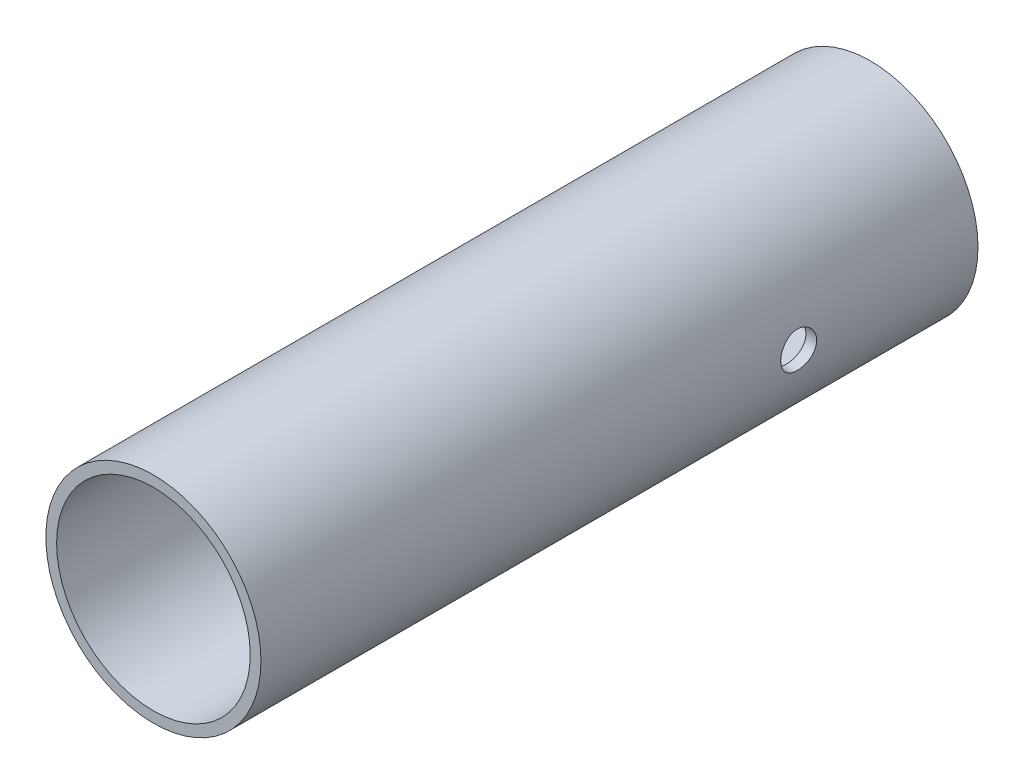
SolidWorks part; units mm, degrees
ref_plane "Płaszczyzna przednia" through (0, 0, 0) normal (0, 0, 1) x (1, 0, 0)
ref_plane "Płaszczyzna górna" through (0, 0, 0) normal (0, 1, 0) x (1, 0, 0)
ref_plane "Płaszczyzna prawa" through (0, 0, 0) normal (1, 0, 0) x (0, 0, -1)
sketch "Szkic2" plane through (0, 0, 0) normal (0, 0, 1) x (1, 0, 0)
  circle A0 centre (0, 0) radius 30
  circle A1 centre (0, 0) radius 27
  dimension "D1" = 60
  dimension "D2" = 54
extrude "Dodanie-wyciągnięcie4" add sketch "Szkic2" along normal blind 200
hole_wizard "Otwory ustalające Ø10.0mm1" positions "Szkic 3D2" profile "Szkic4" hole size "Ø10.0" standard "BSI" end condition through all
sketch3d "Szkic 3D2"
  point P0 (30, 0, 50)
sketch "Szkic4" plane through (30, 0, 50) normal (0, 1, 0) x (0, 0, -1)
  line L0 (0, 0) -> (0, 60)
  line L1 (0, 60) -> (5, 60)
  line L2 (5, 60) -> (5, 0.025)
  line L3 (5, 0.025) -> (5.025, 0)
  line L5 (5.025, 0) -> (0, 0)
  line L6 (-5, 0.025) -> (-5.025, 0) construction
  line L11 (0, -6.35) -> (0, 107.95) construction
  dimension "Średnica otworu na wylot" = 10
  dimension "Głębokość otworu na wylot" = 60
  dimension "Średnica zewnętrznego pogłębienia stożkowego" = 10.05
  dimension "Kąt zewnętrznego pogłębienia stożkowego" = 90
